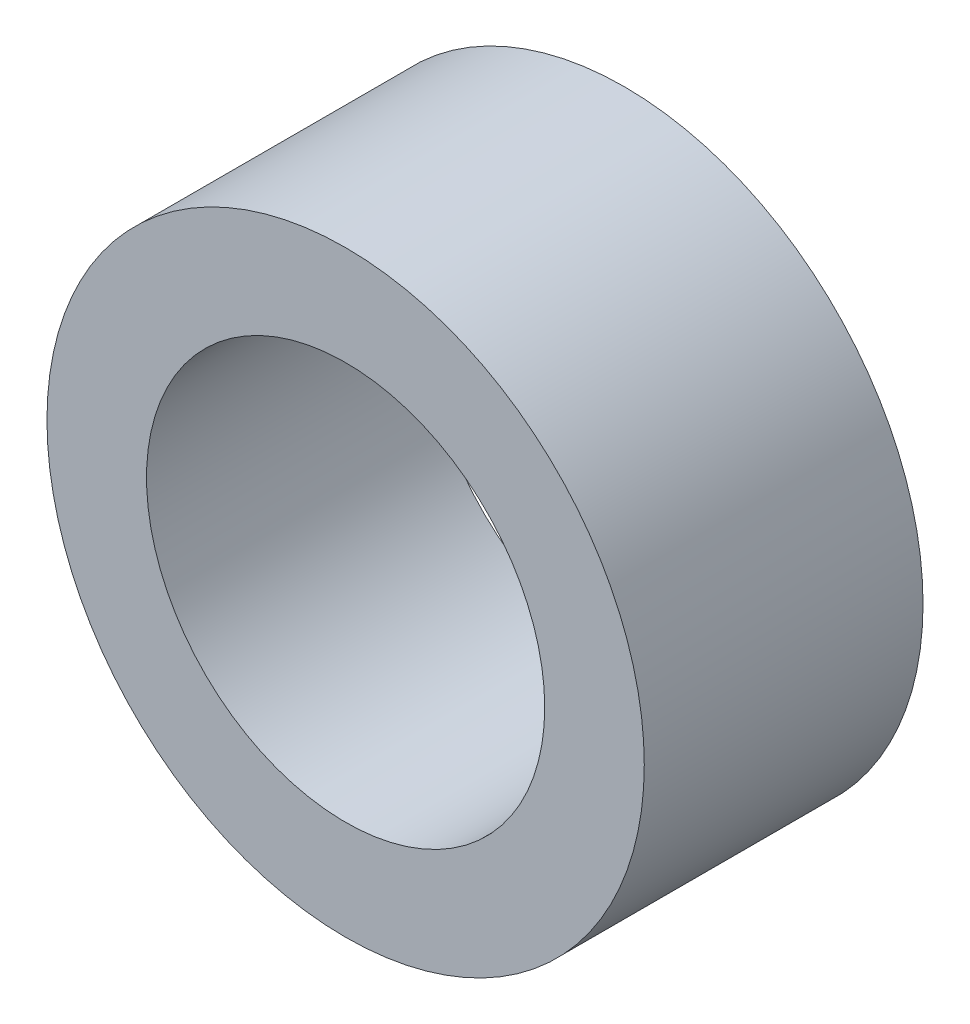
SolidWorks part; units mm, degrees
ref_plane "Front Plane" through (0, 0, 0) normal (0, 0, 1) x (1, 0, 0)
ref_plane "Top Plane" through (0, 0, 0) normal (0, 1, 0) x (1, 0, 0)
ref_plane "Right Plane" through (0, 0, 0) normal (1, 0, 0) x (0, 0, -1)
sketch "Sketch1" plane through (0, 0, 0) normal (0, 0, 1) x (1, 0, 0)
  circle A0 centre (0, 0) radius 20
  circle A1 centre (0, 0) radius 30
  dimension "D1" = 60
  dimension "D2" = 40
extrude "Boss-Extrude1" add sketch "Sketch1" along normal mid plane 28
